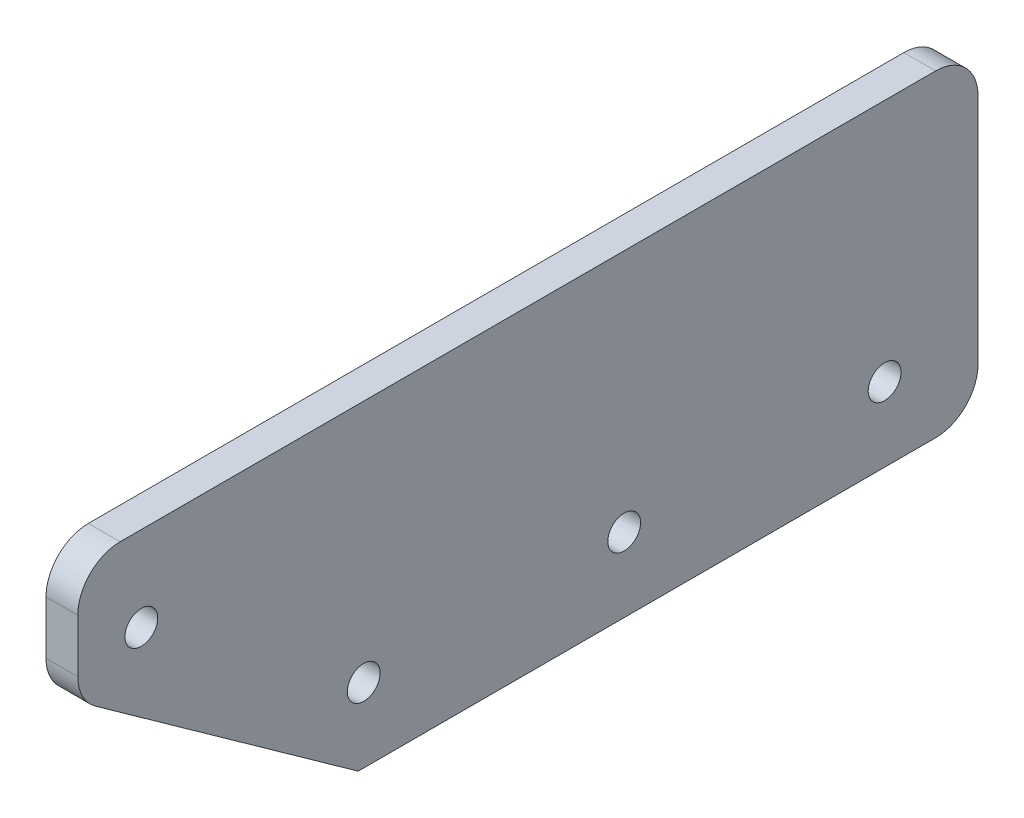
SolidWorks part; units mm, degrees
ref_plane "Ebene vorne" through (0, 0, 0) normal (0, 0, 1) x (1, 0, 0)
ref_plane "Ebene oben" through (0, 0, 0) normal (0, 1, 0) x (1, 0, 0)
ref_plane "Ebene rechts" through (0, 0, 0) normal (1, 0, 0) x (0, 0, -1)
sketch "Skizze1" plane through (0, 0, 0) normal (1, 0, 0) x (0, 0, -1)
  line L1 (0, 0) -> (85, 0)
  line L2 (0, 0) -> (0, 30)
  line L3 (0, 30) -> (85, 30)
  line L4 (85, 0) -> (85, 30)
  dimension "D1" = 85
  dimension "D2" = 30
extrude "Aufsatz-Linear austragen1" add sketch "Skizze1" along normal blind 3
sketch "Skizze2" plane through (3, 0, 0) normal (1, 0, 0) x (0, 0, -1)
  line L0 (6, 0) -> (6, 22) construction
  line L1 (0, 0) -> (85, 0) construction
  line L2 (27, 0) -> (27, 7) construction
  line L3 (51.5919, 0) -> (51.5919, 7) construction
  line L4 (76.1837, 0) -> (76.1837, 7) construction
  line L5 (76.1837, 7) -> (51.5919, 7) construction
  line L6 (51.5919, 7) -> (27, 7) construction
  line L7 (0, 30) -> (0, 0) construction
  circle A0 centre (6, 22) radius 1.55
  circle A1 centre (27, 7) radius 1.55
  circle A2 centre (51.5919, 7) radius 1.55
  circle A3 centre (76.1837, 7) radius 1.55
  point P16 (0, 0)
  point P17 (74.0084, 7)
  point P18 (76.1837, 7)
  dimension "D6" = 3.1
  dimension "D1" = 21
  dimension "D3" = 15
  dimension "D4" = 7
  dimension "D5" = 6
  dimension "D7" = 49.1837
extrude "Schnitt-Linear austragen1" cut sketch "Skizze2" against normal through all
sketch "Skizze3" plane through (3, 0, 0) normal (1, 0, 0) x (0, 0, -1)
  line L0 (0, 18.9123) -> (26.4772, 0)
  line L1 (0, 30) -> (0, 0) construction
  line L2 (0, 0) -> (85, 0) construction
  line L3 (26.4772, 0) -> (0, 0)
  line L4 (0, 0) -> (0, 18.9123)
  line L5 (6, 22) -> (27, 7) construction
  dimension "D1" = 6
extrude "Schnitt-Linear austragen2" cut sketch "Skizze3" against normal through all
fillet "Verrundung1" radius 4 4 edges at (1.5, 18.9123, 0) (1.5, 0, -85) (1.5, 30, 0) (1.5, 30, -85)
